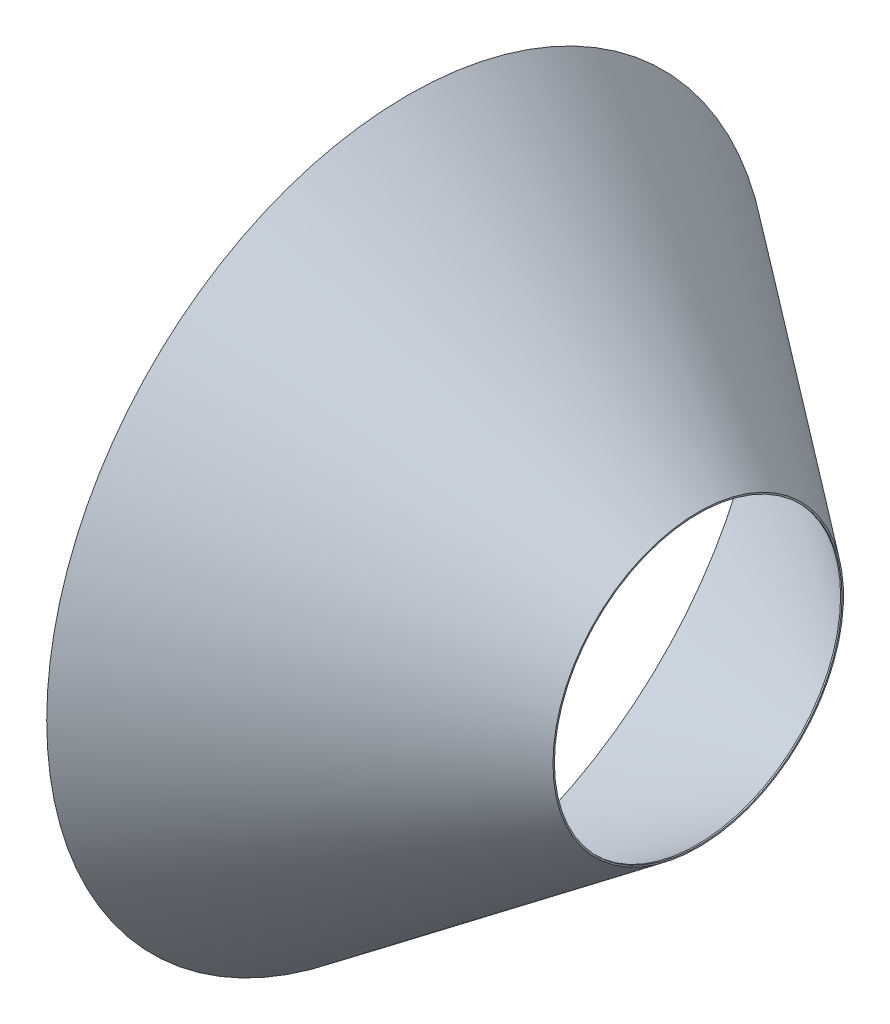
SolidWorks part; units mm, degrees
material "Gray Cast Iron"
ref_plane "Front Plane" through (0, 0, 0) normal (0, 0, 1) x (1, 0, 0)
ref_plane "Top Plane" through (0, 0, 0) normal (0, 1, 0) x (1, 0, 0)
ref_plane "Right Plane" through (0, 0, 0) normal (1, 0, 0) x (0, 0, -1)
sketch "Sketch1" plane through (0, 0, 0) normal (0, 0, 1) x (1, 0, 0)
  line L8 (0, 0) -> (0, 251)
  line L10 (202, 251) -> (202, 150)
  line L11 (0, 0) -> (202, 150)
  line L13 (0, 251) -> (202, 251)
  line L14 (201, 249.7582) -> (201, 151)
  line L15 (201, 151) -> (0.5, 2.1139)
  line L16 (0.5, 2.1139) -> (1, 249.7582)
  line L18 (1, 249.7582) -> (201, 249.7582)
  dimension "D1" = 251
  dimension "D2" = 101
  dimension "D3" = 202
revolve "Revolve2" add sketch "Sketch1" angle 360 about L13
sketch "Sketch4" plane through (202, 0, 0) normal (1, 0, 0) x (0, 0, -1)
  circle A0 centre (0, 251) radius 100
extrude "Cut-Extrude2" cut sketch "Sketch4" against normal blind 10
sketch "Sketch5" plane through (0, 0, 0) normal (-1, 0, 0) x (0, 0, 1)
  circle A1 centre (0, 251) radius 250
extrude "Cut-Extrude4" cut sketch "Sketch5" against normal blind 1
sketch "Sketch6" plane through (1, 0, 0) normal (-1, 0, 0) x (0, 0, 1)
  circle A0 centre (0, 251) radius 1.2418
extrude "Cut-Extrude5" cut sketch "Sketch6" against normal blind 201
